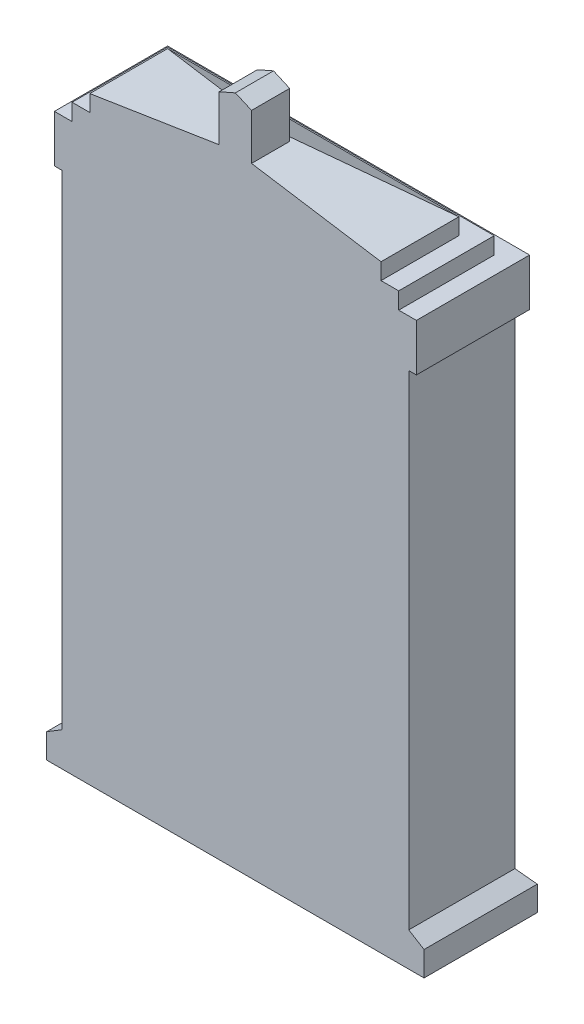
SolidWorks part; units mm, degrees
ref_plane "Front Plane" through (0, 0, 0) normal (0, 0, 1) x (1, 0, 0)
ref_plane "Top Plane" through (0, 0, 0) normal (0, 1, 0) x (1, 0, 0)
ref_plane "Right Plane" through (0, 0, 0) normal (1, 0, 0) x (0, 0, -1)
sketch "Sketch1" plane through (0, 0, 0) normal (0, 0, 1) x (1, 0, 0)
  line L0 (12.446, -21.6881) -> (13.5445, -22.358)
  line L1 (13.5445, -22.358) -> (13.5445, -24.13)
  line L2 (-12.446, 17.0133) -> (-12.446, 24.13) construction
  line L4 (-12.446, -21.6881) -> (-12.446, 13.0885) construction
  line L5 (-12.446, -24.13) -> (12.446, 24.13) construction
  line L6 (-12.446, 24.13) -> (12.446, -24.13) construction
  line L7 (-12.446, 17.0133) -> (-12.446, 24.13) construction
  line L8 (13.5445, -24.13) -> (-13.5445, -24.13)
  line L9 (12.446, 24.13) -> (-12.446, -24.13) construction
  line L10 (12.446, -24.13) -> (-12.446, 24.13) construction
  line L11 (-13.5445, -22.358) -> (-13.5445, -24.13)
  line L13 (-12.446, -21.6881) -> (-13.5445, -22.358)
  line L14 (0, 0) -> (0, -24.13) construction
  line L15 (-12.446, -21.6881) -> (-12.446, 13.0885)
  line L16 (-12.446, 13.0885) -> (-12.9947, 13.0885)
  line L17 (-12.9947, 13.0885) -> (-12.9947, 16.4824)
  line L18 (-12.9947, 16.4824) -> (-11.7247, 16.4824)
  line L19 (-11.7247, 16.4824) -> (-11.7247, 17.6836)
  line L20 (-10.4547, 17.6836) -> (-10.4547, 18.8599)
  line L22 (-11.7247, 17.6836) -> (-10.4547, 17.6836)
  line L23 (-10.4547, 18.8599) -> (0, 20.5057)
  line L26 (-12.446, -21.6881) -> (-12.446, 13.0885) construction
  line L30 (12.446, -21.9231) -> (12.446, 13.0885) construction
  line L31 (12.446, -21.9231) -> (12.446, 13.0885) construction
  line L33 (10.4547, 18.8599) -> (0, 20.5057)
  line L34 (11.7247, 17.6836) -> (10.4547, 17.6836)
  line L35 (10.4547, 17.6836) -> (10.4547, 18.8599)
  line L36 (12.446, 17.0133) -> (12.446, 24.13) construction
  line L37 (12.446, 17.0133) -> (12.446, 24.13) construction
  line L38 (11.7247, 16.4824) -> (11.7247, 17.6836)
  line L39 (12.9947, 16.4824) -> (11.7247, 16.4824)
  line L40 (12.9947, 13.0885) -> (12.9947, 16.4824)
  line L41 (12.446, 13.0885) -> (12.9947, 13.0885)
  line L42 (12.446, -21.6881) -> (12.446, 13.0885)
  point P0 (0, 0)
  point P10 (0, 24.13)
  dimension "D1" = 48.26
  dimension "D2" = 24.892
  dimension "D3" = 21.6881
  dimension "D4" = 1.27
  dimension "D5" = 1.27
sketch "Sketch3" plane through (0, 0, 0) normal (0, 0, 1) x (1, 0, 0)
  line L0 (0, 24.1813) -> (0, -24.13) construction
  line L1 (-9.652, 12.2966) -> (-0.508, 12.2966)
  line L2 (-9.652, 12.2966) -> (-9.652, -21.6881)
  line L3 (-9.652, -21.6881) -> (-0.508, -21.6881)
  line L4 (9.652, 12.2966) -> (9.652, -21.6881)
  line L5 (0, 12.2966) -> (0, -21.8818) construction
  line L6 (0.508, 12.2966) -> (0.508, -21.6881)
  line L7 (-0.508, 12.2966) -> (-0.508, -21.6881)
  line L8 (0.508, 12.2966) -> (9.652, 12.2966)
  line L9 (0.508, -21.6881) -> (9.652, -21.6881)
  dimension "D1" = 9.652
  dimension "D2" = 9.652
  dimension "D3" = 0.508
  dimension "D4" = 21.6881
sketch "Sketch2" plane through (0, 0, 0) normal (0, 0, 1) x (1, 0, 0)
  line L0 (0, -24.13) -> (0, 24.1813) construction
  line L1 (-8.3394, -20.5457) -> (-1.613, -20.5457)
  line L2 (-8.3394, -20.5457) -> (-8.3394, -13.2866)
  line L3 (-8.3394, -13.2866) -> (-1.613, -13.2866)
  line L4 (-1.613, -20.5457) -> (-1.613, -13.2866)
  line L5 (-8.3394, -12.3976) -> (-1.613, -12.3976)
  line L6 (-8.3394, -12.3976) -> (-8.3394, -5.1385)
  line L7 (-8.3394, -5.1385) -> (-1.613, -5.1385)
  line L8 (-1.613, -12.3976) -> (-1.613, -5.1385)
  line L9 (-8.3394, -4.2495) -> (-1.613, -4.2495)
  line L10 (-8.3394, -4.2495) -> (-8.3394, 3.0096)
  line L11 (-8.3394, 3.0096) -> (-1.613, 3.0096)
  line L12 (-1.613, -4.2495) -> (-1.613, 3.0096)
  line L13 (1.613, 11.1448) -> (1.613, 7.7503)
  line L14 (3.5165, 7.7503) -> (1.613, 7.7503)
  line L15 (3.5165, 11.1448) -> (3.5165, 7.7503)
  line L16 (3.5165, 11.1448) -> (1.613, 11.1448)
  line L17 (4.0245, 11.1448) -> (4.0245, 7.7503)
  line L18 (5.9279, 7.7503) -> (4.0245, 7.7503)
  line L19 (5.9279, 11.1448) -> (5.9279, 7.7503)
  line L20 (5.9279, 11.1448) -> (4.0245, 11.1448)
  line L21 (1.613, -4.2495) -> (1.613, 3.0096)
  line L22 (8.3394, 3.0096) -> (1.613, 3.0096)
  line L23 (8.3394, -4.2495) -> (8.3394, 3.0096)
  line L24 (8.3394, -4.2495) -> (1.613, -4.2495)
  line L25 (1.613, -12.3976) -> (1.613, -5.1385)
  line L26 (8.3394, -5.1385) -> (1.613, -5.1385)
  line L27 (8.3394, -12.3976) -> (8.3394, -5.1385)
  line L28 (8.3394, -12.3976) -> (1.613, -12.3976)
  line L29 (1.613, -20.5457) -> (1.613, -13.2866)
  line L30 (8.3394, -13.2866) -> (1.613, -13.2866)
  line L31 (8.3394, -20.5457) -> (8.3394, -13.2866)
  line L32 (8.3394, -20.5457) -> (1.613, -20.5457)
  line L33 (6.4359, 11.1448) -> (6.4359, 7.7503)
  line L34 (8.3394, 7.7503) -> (6.4359, 7.7503)
  line L35 (8.3394, 11.1448) -> (8.3394, 7.7503)
  line L36 (8.3394, 11.1448) -> (6.4359, 11.1448)
  line L37 (-8.3394, 7.5217) -> (-1.613, 7.5217) construction
  line L38 (-1.613, 3.8986) -> (-1.613, 7.2931)
  line L39 (-3.5165, 7.2931) -> (-1.613, 7.2931)
  line L40 (-3.5165, 3.8986) -> (-3.5165, 7.2931)
  line L41 (-3.5165, 3.8986) -> (-1.613, 3.8986)
  line L42 (-4.0245, 3.8986) -> (-4.0245, 7.2931)
  line L43 (-5.9279, 7.2931) -> (-4.0245, 7.2931)
  line L44 (-5.9279, 3.8986) -> (-5.9279, 7.2931)
  line L45 (-5.9279, 3.8986) -> (-4.0245, 3.8986)
  line L46 (-6.4359, 3.8986) -> (-6.4359, 7.2931)
  line L47 (-8.3394, 7.2931) -> (-6.4359, 7.2931)
  line L48 (-8.3394, 3.8986) -> (-8.3394, 7.2931)
  line L49 (-8.3394, 3.8986) -> (-6.4359, 3.8986)
  line L50 (8.3394, 7.5217) -> (1.613, 7.5217) construction
  line L51 (-8.3394, 11.1448) -> (-6.4359, 11.1448)
  line L52 (8.3394, 3.8986) -> (6.4359, 3.8986)
  line L53 (8.3394, 3.8986) -> (8.3394, 7.2931)
  line L54 (8.3394, 7.2931) -> (6.4359, 7.2931)
  line L55 (6.4359, 3.8986) -> (6.4359, 7.2931)
  line L56 (5.9279, 3.8986) -> (4.0245, 3.8986)
  line L57 (5.9279, 3.8986) -> (5.9279, 7.2931)
  line L58 (5.9279, 7.2931) -> (4.0245, 7.2931)
  line L59 (4.0245, 3.8986) -> (4.0245, 7.2931)
  line L60 (3.5165, 3.8986) -> (1.613, 3.8986)
  line L61 (3.5165, 3.8986) -> (3.5165, 7.2931)
  line L62 (3.5165, 7.2931) -> (1.613, 7.2931)
  line L63 (1.613, 3.8986) -> (1.613, 7.2931)
  line L64 (-8.3394, 11.1448) -> (-8.3394, 7.7503)
  line L65 (-8.3394, 7.7503) -> (-6.4359, 7.7503)
  line L66 (-6.4359, 11.1448) -> (-6.4359, 7.7503)
  line L67 (-5.9279, 11.1448) -> (-4.0245, 11.1448)
  line L68 (-5.9279, 11.1448) -> (-5.9279, 7.7503)
  line L69 (-5.9279, 7.7503) -> (-4.0245, 7.7503)
  line L70 (-4.0245, 11.1448) -> (-4.0245, 7.7503)
  line L71 (-3.5165, 11.1448) -> (-1.613, 11.1448)
  line L72 (-3.5165, 11.1448) -> (-3.5165, 7.7503)
  line L73 (-3.5165, 7.7503) -> (-1.613, 7.7503)
  line L74 (-1.613, 11.1448) -> (-1.613, 7.7503)
  dimension "D1" = 0.889
  dimension "D2" = 0.889
  dimension "D3" = 0.889
  dimension "D5" = 6.7263
  dimension "D6" = 1.613
  dimension "D7" = 0.508
  dimension "D8" = 0.508
  dimension "D9" = 0.2286
extrude "Boss-Extrude1" add sketch "Sketch1" along normal blind 7.62
extrude "Cut-Extrude3" cut sketch "Sketch3" along normal blind 1.27
extrude "Cut-Extrude4" cut sketch "Sketch2" along normal blind 2.032
sketch "Sketch5" plane through (0, 0, 2.032) normal (0, 0, -1) x (-1, 0, 0)
  line L0 (-8.3394, -0.6199) -> (-1.613, -0.6199) construction
  line L1 (-8.3394, -4.2495) -> (-8.3394, 3.0096) construction
  line L2 (-1.613, 3.0096) -> (-1.613, -4.2495) construction
  line L3 (1.613, -0.6199) -> (3.7944, -0.6199) construction
  line L4 (-7.3197, -3.6987) -> (-2.6327, -3.6987)
  line L5 (-7.3197, -3.6987) -> (-7.3197, 2.4589)
  line L6 (-7.3197, 2.4589) -> (-2.6327, 2.4589)
  line L7 (-2.6327, -3.6987) -> (-2.6327, 2.4589)
  line L8 (-7.3197, -3.6987) -> (-2.6327, 2.4589) construction
  line L9 (-7.3197, 2.4589) -> (-2.6327, -3.6987) construction
  line L12 (1.613, 3.0096) -> (1.613, -4.2495) construction
  line L13 (8.3394, -4.2495) -> (8.3394, 3.0096) construction
  line L14 (6.158, -0.6199) -> (8.3394, -0.6199) construction
  point P6 (-4.9762, -0.6199)
extrude "Boss-Extrude3" add sketch "Sketch5" along normal blind 0.508
sketch "Sketch6" plane through (0, 0, 0) normal (0, 0, -1) x (-1, 0, 0)
  line L0 (-12.9947, 14.7855) -> (12.9947, 14.7855) construction
  line L1 (-12.9947, 13.0885) -> (-12.9947, 16.4824) construction
  line L2 (12.9947, 16.4824) -> (12.9947, 13.0885) construction
  line L3 (0, 24.1813) -> (0, -24.13) construction
  line L4 (12.446, -24.13) -> (-12.446, -24.13) construction
  line L6 (12.4867, 13.5965) -> (-12.4867, 13.5965)
  line L7 (12.4867, 13.5965) -> (12.4867, 15.9744)
  line L8 (12.4867, 15.9744) -> (-12.4867, 15.9744)
  line L9 (-12.4867, 13.5965) -> (-12.4867, 15.9744)
  line L10 (12.4867, 13.5965) -> (-12.4867, 15.9744) construction
  line L11 (12.4867, 15.9744) -> (-12.4867, 13.5965) construction
  line L12 (-11.7247, 16.4824) -> (11.8613, 16.4824)
  line L13 (-11.7247, 16.4824) -> (-11.7247, 24.6043)
  line L14 (-11.7247, 24.6043) -> (11.8613, 24.6043)
  line L15 (11.8613, 16.4824) -> (11.8613, 24.6043)
  point P11 (0, 14.7855)
  dimension "D1" = 0.508
  dimension "D2" = 0.508
extrude "Cut-Extrude5" [suppressed] cut sketch "Sketch6" against normal blind 0.508
sketch "Sketch7" [suppressed] plane through (0, 0, 0.508) normal (0, 0, -1) x (-1, 0, 0)
  line L1 (-10.4547, 17.6836) -> (10.8159, 17.6836)
  line L2 (-10.4547, 17.6836) -> (-10.4547, 26.0002)
  line L3 (-10.4547, 26.0002) -> (10.8159, 26.0002)
  line L4 (10.8159, 17.6836) -> (10.8159, 26.0002)
extrude "Cut-Extrude6" [suppressed] cut sketch "Sketch7" against normal blind 0.508
sketch "Sketch8" plane through (0, 0, 0) normal (0, 0, -1) x (-1, 0, 0)
  line L1 (-13.5445, -24.13) -> (13.5445, -24.13)
  line L2 (-13.5445, -24.13) -> (-13.5445, -22.358)
  line L3 (-13.5445, -22.358) -> (13.5445, -22.358)
  line L4 (13.5445, -24.13) -> (13.5445, -22.358)
  point P0 (0, -23.0816)
extrude "Boss-Extrude4" add sketch "Sketch8" along normal blind 0.508 contours L3 L4 L1 L2
sketch "Sketch9" plane through (0, 0, 0) normal (1, 0, 0) x (0, 0, -1)
  line L0 (0.508, -22.358) -> (0, -21.6881)
  line L1 (0, -21.6881) -> (0, -22.358)
  line L2 (-7.62, -22.358) -> (0, -22.358) construction
  line L3 (0, -22.358) -> (0.508, -22.358)
extrude "Boss-Extrude5" add sketch "Sketch9" along normal up to surface and the other way up to surface up to face at (12.9952, -22.0231, 3.81) other way up to face at (-12.9952, -22.0231, 3.81)
sketch "Sketch10" plane through (0, 0, 0) normal (0, 0, -1) x (-1, 0, 0)
  line L1 (-12.9947, 13.0885) -> (12.9947, 13.0885)
  line L2 (-12.9947, 13.0885) -> (-12.9947, 16.4824)
  line L3 (-12.9947, 16.4824) -> (12.9947, 16.4824)
  line L4 (12.9947, 13.0885) -> (12.9947, 16.4824)
extrude "Boss-Extrude6" add sketch "Sketch10" along normal blind 0.508
sketch "Sketch11" plane through (0, 0, 0) normal (0, 0, -1) x (-1, 0, 0)
  line L1 (-11.7247, 16.4824) -> (11.7247, 16.4824)
  line L2 (-11.7247, 16.4824) -> (-11.7247, 25.6712)
  line L3 (-11.7247, 25.6712) -> (11.7247, 25.6712)
  line L4 (11.7247, 16.4824) -> (11.7247, 25.6712)
extrude "Cut-Extrude7" cut sketch "Sketch11" against normal blind 0.762
chamfer "Chamfer1" [suppressed] distance 0.508 angle 45
sketch "Sketch12" plane through (0, 0, 0.762) normal (0, 0, -1) x (-1, 0, 0)
  line L0 (10.4547, 18.8599) -> (10.4547, 17.6836) construction
  line L1 (-10.4547, 17.6836) -> (10.4547, 17.6836)
  line L2 (-10.4547, 17.6836) -> (-10.4547, 25.0942)
  line L3 (-10.4547, 25.0942) -> (10.4547, 25.0942)
  line L4 (10.4547, 17.6836) -> (10.4547, 25.0942)
extrude "Cut-Extrude8" cut sketch "Sketch12" against normal blind 1.27
sketch "Sketch13" plane through (0, 0, 2.032) normal (0, 0, -1) x (-1, 0, 0)
  line L0 (-10.4547, 18.8599) -> (10.4547, 18.8599) construction
ref_plane "Plane1" through (0, 13.2651, -7.6586) normal (0, -0.866, 0.5) x (1, 0, 0)
sketch "Sketch14" plane through (0, 13.2651, -7.6586) normal (0, -0.866, 0.5) x (1, 0, 0)
  line L0 (-10.4547, 15.4409) -> (-10.4547, 10.6015) construction
  line L1 (10.4547, 11.1897) -> (-10.4547, 11.1897)
  line L2 (10.4547, 11.1897) -> (10.4547, 15.2971)
  line L3 (10.4547, 15.2971) -> (-10.4547, 15.2971)
  line L4 (-10.4547, 11.1897) -> (-10.4547, 15.2971)
extrude "Cut-Extrude9" cut sketch "Sketch14" against normal through all
sketch "Sketch15" plane through (0, 0, 7.62) normal (0, 0, 1) x (1, 0, 0)
  line L2 (1.1592, 23.6198) -> (1.1592, 19.5828)
  line L3 (1.1592, 19.5828) -> (-1.1592, 19.5828)
  line L4 (-1.1592, 23.6198) -> (-1.1592, 19.5828)
  line L5 (0.9468, 23.7133) -> (-1.1592, 19.5828) construction
  line L6 (1.1592, 19.5828) -> (-0.9468, 23.7133) construction
  line L7 (1.1592, 23.6198) -> (0, 24.13)
  line L8 (0, 24.13) -> (-1.1592, 23.6198)
  point P0 (0, 21.8564)
extrude "Boss-Extrude8" add sketch "Sketch15" against normal up to vertex (2.7374 mm away) up to point (0, 20.5057, 4.8826)
sketch "Sketch17" plane through (0, 0, -0.508) normal (0, 0, -1) x (-1, 0, 0)
  line L0 (-12.9947, 14.7855) -> (12.9947, 14.7855) construction
  line L1 (-12.9947, 16.4824) -> (-12.9947, 13.0885) construction
  line L2 (12.9947, 13.0885) -> (12.9947, 16.4824) construction
  line L3 (12.9947, 16.4824) -> (-12.9947, 16.4824) construction
  line L4 (-12.4867, 15.9744) -> (12.4867, 15.9744)
  line L5 (-12.4867, 15.9744) -> (-12.4867, 13.5965)
  line L6 (-12.4867, 13.5965) -> (12.4867, 13.5965)
  line L7 (12.4867, 15.9744) -> (12.4867, 13.5965)
  line L8 (-12.4867, 15.9744) -> (12.4867, 13.5965) construction
  line L9 (-12.4867, 13.5965) -> (12.4867, 15.9744) construction
  point P6 (0, 14.7855)
  dimension "D1" = 0.508
  dimension "D2" = 0.508
extrude "Cut-Extrude11" cut sketch "Sketch17" against normal blind 0.508
sketch "Sketch18" plane through (0, 0, 0) normal (0, 0, -1) x (-1, 0, 0)
  line L0 (-12.4867, 13.7763) -> (12.4867, 13.7763) construction
  line L1 (-12.4867, 15.9744) -> (-12.4867, 13.5965) construction
  line L2 (12.4867, 13.5965) -> (12.4867, 15.9744) construction
  text T0 "MACGREGOR" font "Gill Sans MT" height in points 8
sketch "Sketch19" plane through (0, 0, 1.524) normal (0, 0, -1) x (-1, 0, 0)
  line L0 (-7.3197, -2.6293) -> (-2.6327, -2.6293) construction
  line L1 (-7.3197, 2.4589) -> (-7.3197, -3.6987) construction
  line L2 (-2.6327, -3.6987) -> (-2.6327, 2.4589) construction
  text T0 "E" font "Gill Sans MT" height in points 16
extrude "Cut-Extrude12" cut sketch "Sketch19" against normal blind 0.508
extrude "Cut-Extrude13" cut sketch "Sketch18" against normal blind 0.254
